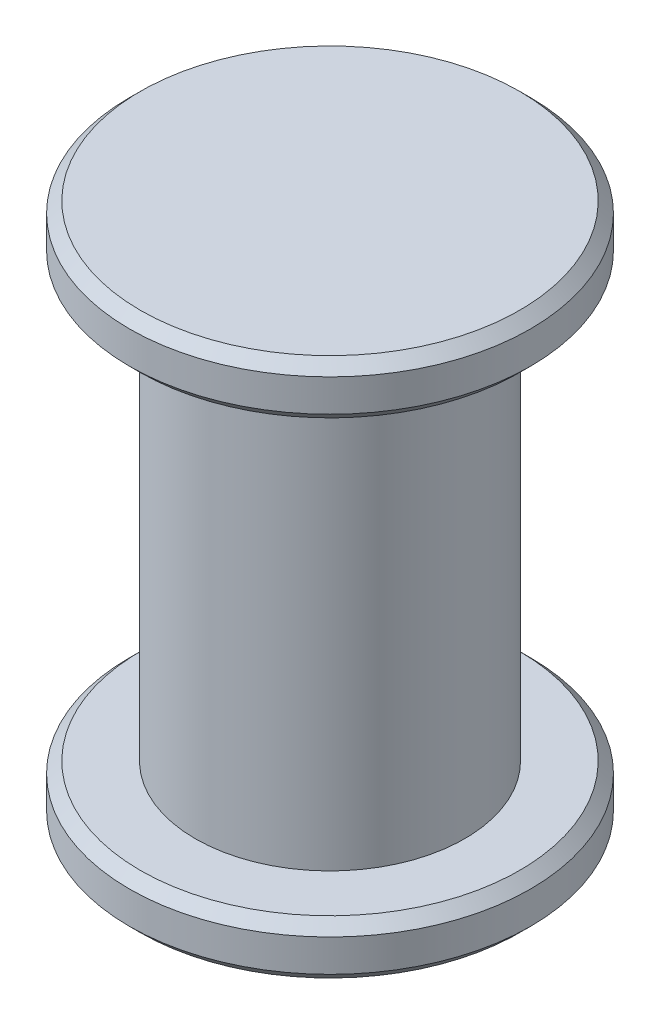
SolidWorks part; units mm, degrees
ref_plane "Front Plane" through (0, 0, 0) normal (0, 0, 1) x (1, 0, 0)
ref_plane "Top Plane" through (0, 0, 0) normal (0, 1, 0) x (1, 0, 0)
ref_plane "Right Plane" through (0, 0, 0) normal (1, 0, 0) x (0, 0, -1)
sketch "Sketch2" plane through (0, 0, 0) normal (0, 1, 0) x (1, 0, 0)
  circle A0 centre (0, 0) radius 0.25
  dimension "D1" = 0.5
extrude "Boss-Extrude1" add sketch "Sketch2" along normal blind 0.8
sketch "Sketch3" plane through (0, 0.8, 0) normal (0, 1, 0) x (1, 0, 0)
  circle A0 centre (0, 0) radius 0.3719
extrude "Boss-Extrude2" add sketch "Sketch3" along normal blind 0.1
sketch "Sketch4" plane through (0, 0, 0) normal (0, -1, 0) x (1, 0, 0)
  circle A0 centre (0, 0) radius 0.3719
extrude "Boss-Extrude3" add sketch "Sketch4" along normal blind 0.1
chamfer "Chamfer1" distance 0.02 angle 45 1 edges at (0, 0.9, 0.3719)
chamfer "Chamfer2" distance 0.02 angle 45 2 edges at (0, 0, -0.3719) (0, 0.8, 0.3719)
chamfer "Chamfer3" distance 0.02 angle 45 1 edges at (0, -0.1, -0.3719)
